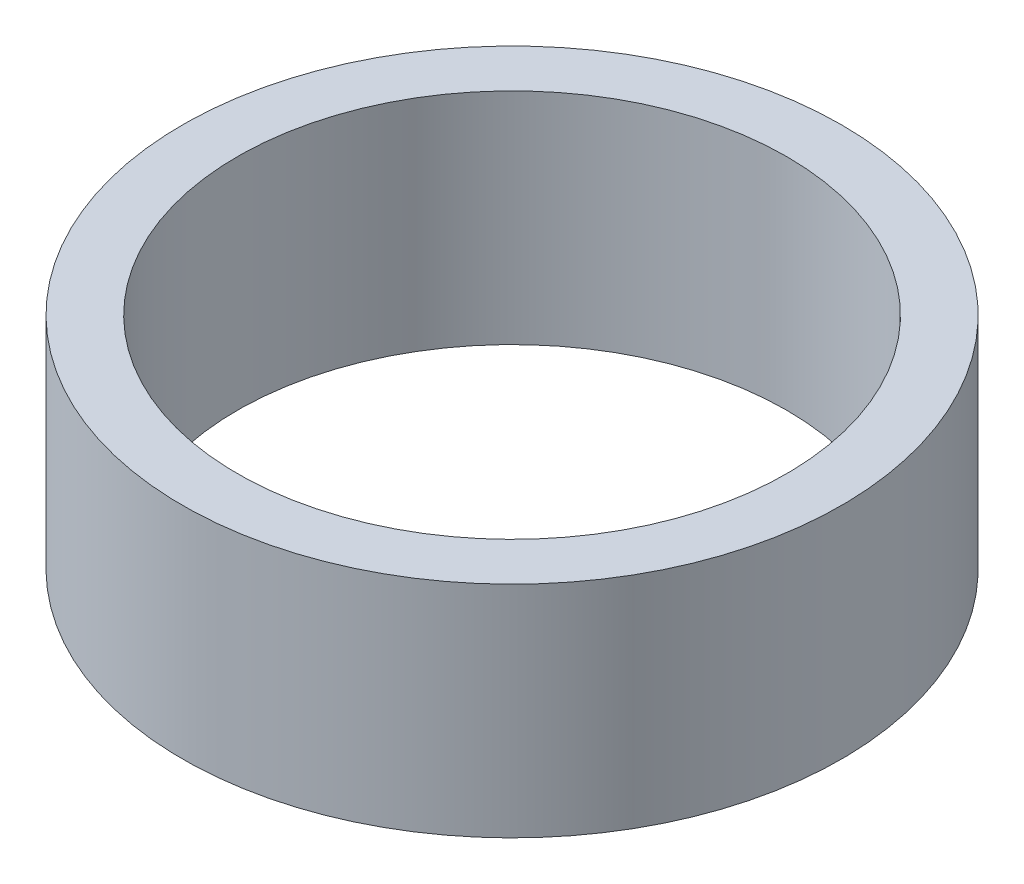
SolidWorks part; units mm, degrees
material "Copper"
ref_plane "Front Plane" through (0, 0, 0) normal (0, 0, 1) x (1, 0, 0)
ref_plane "Top Plane" through (0, 0, 0) normal (0, 1, 0) x (1, 0, 0)
ref_plane "Right Plane" through (0, 0, 0) normal (1, 0, 0) x (0, 0, -1)
sketch "Sketch1" plane through (0, 0, 0) normal (0, 0, 1) x (1, 0, 0)
  line L0 (0, 0) -> (1.25, 0) construction
  line L1 (1.25, 0) -> (1.5, 0)
  line L2 (1.25, 0) -> (1.25, 1)
  line L3 (1.25, 1) -> (1.5, 1)
  line L4 (1.5, 0) -> (1.5, 1)
  line L5 (0, 0) -> (0, 7.7064) construction
  dimension "D1" = 1
  dimension "D2" = 3
  dimension "D3" = 2.5
revolve "Revolve1" add sketch "Sketch1" angle 360 about L5
